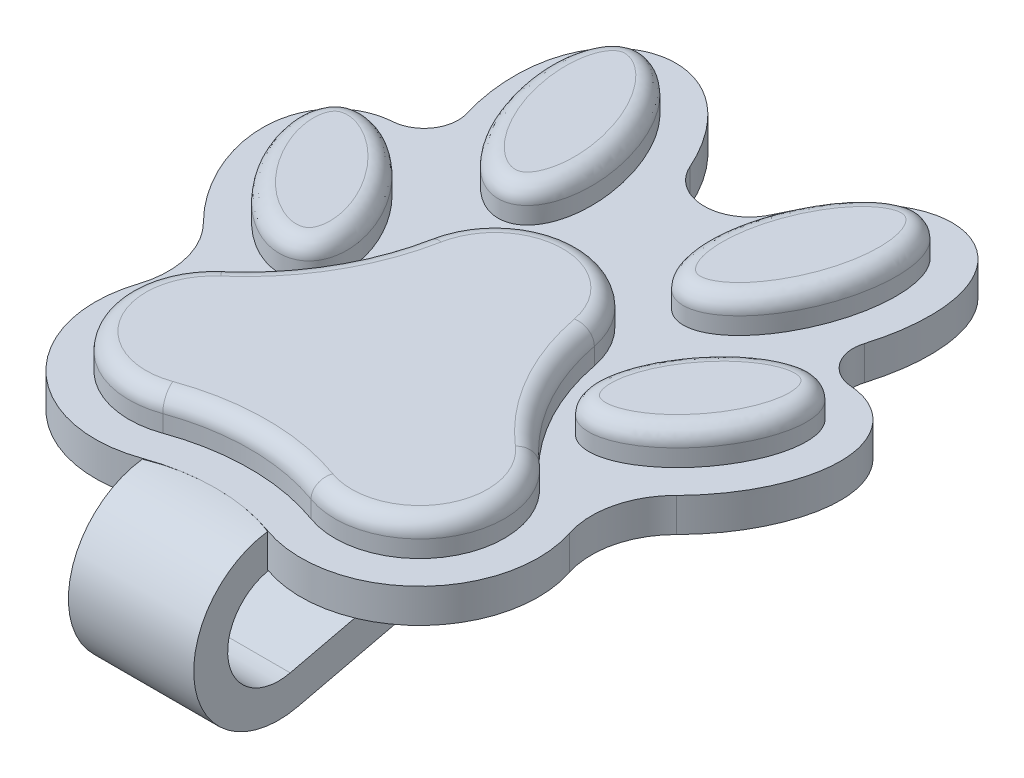
SolidWorks part; units mm, degrees
ref_plane "Front Plane" through (0, 0, 0) normal (0, 0, 1) x (1, 0, 0)
ref_plane "Top Plane" through (0, 0, 0) normal (0, 1, 0) x (1, 0, 0)
ref_plane "Right Plane" through (0, 0, 0) normal (1, 0, 0) x (0, 0, -1)
sketch "Sketch3" plane through (0, 0, 0) normal (0, 1, 0) x (1, 0, 0)
  line L0 (0, 0) -> (0, -27.3757) construction
  line L1 (0, 5) -> (-6.0622, -5.5) construction
  arc A0 (4.9097, 5.9458) -> (-4.9097, 5.9458) centre (0, 5) ccw
  arc A1 (4.3698, -10.2049) -> (9.3361, -1.721) centre (6.0622, -5.5) ccw
  arc A2 (-9.3361, -1.721) -> (-4.3698, -10.2049) centre (-6.0622, -5.5) ccw
  arc A3 (-4.9097, 5.9458) -> (-9.3361, -1.721) centre (-18.1955, 8.5052) cw
  arc A4 (4.9097, 5.9458) -> (9.3361, -1.721) centre (18.1955, 8.5052) ccw
  arc A5 (4.3698, -10.2049) -> (-4.3698, -10.2049) centre (0, -22.3528) ccw
  ellipse E0 centre (11.1505, 5.9458) end of major axis (8.0278, 1.7402) minor radius 2.8576
  ellipse E1 centre (6.7977, 16.2233) end of major axis (8.6857, 21.7116) minor radius 3.0528
  ellipse E2 centre (-11.1505, 5.9458) end of major axis (-14.2732, 10.1515) minor radius 2.8576
  ellipse E3 centre (-6.7977, 16.2233) end of major axis (-8.6857, 21.7116) minor radius 3.0528
  point P12 (0, -2)
  dimension "D1" = 5
  dimension "D3" = 10
  dimension "D4" = 12.91
  dimension "D5" = 13.53
  dimension "D2" = 3
extrude "Boss-Extrude1" add sketch "Sketch3" along normal blind 2
sketch "Sketch4" plane through (0, 0, 0) normal (0, -1, 0) x (1, 0, 0)
  arc A0 (2.4233, -18.8956) -> (-2.4381, -18.9289) centre (0, -19.9916) ccw
  arc A1 (11.7264, -15.0458) -> (13.4953, -12.4721) centre (13.6407, -14.4668) cw
  arc A2 (-13.4941, -12.472) -> (-11.7262, -15.0455) centre (-13.6406, -14.4667) cw
  arc A9 (13.9433, -1.7682) -> (12.7166, 3.3278) centre (17.4698, 1.7763) cw
  arc A10 (-13.9449, -1.7693) -> (-12.7167, 3.3281) centre (-17.4699, 1.7767) ccw
  arc A12 (10.6457, 0.2093) -> (3.6928, 12.0868) centre (6.0622, 5.5) ccw
  arc A13 (-3.6928, 12.0868) -> (3.6928, 12.0868) centre (0, 22.3528) ccw
  arc A14 (-3.6928, 12.0868) -> (-10.6457, 0.2093) centre (-6.0622, 5.5) ccw
  arc A15 (12.7166, 3.3278) -> (3.6928, 12.0868) centre (6.0622, 5.5) ccw
  arc A16 (-3.6928, 12.0868) -> (3.6928, 12.0868) centre (0, 22.3528) ccw
  arc A17 (-3.6928, 12.0868) -> (-12.7167, 3.3281) centre (-6.0622, 5.5) ccw
  spline S0 degree 3 poles (-6.6721, -0.2558) (-7.1625, 0.1084) (-7.5206, 0.2889) (-8.2956, 0.5328) (-8.6948, 0.5901) (-9.5056, 0.5933) (-9.905, 0.5391) (-10.6836, 0.3462) (-11.0669, 0.2055) (-11.7925, -0.1333) (-12.1389, -0.3321) (-12.805, -0.7774) (-13.126, -1.0254) (-14.032, -1.814) (-14.5686, -2.4017) (-15.2846, -3.3646) (-15.509, -3.7015) (-15.9166, -4.39) (-16.1008, -4.7427) (-16.4271, -5.4662) (-16.5693, -5.8369) (-16.804, -6.5998) (-16.897, -6.9958) (-17.0137, -7.7923) (-17.0383, -8.193) (-17.0095, -8.7986) (-16.9886, -9.0011) (-16.9229, -9.3979) (-16.878, -9.5933) (-16.7616, -9.9778) (-16.6894, -10.1681) (-16.5172, -10.5349) (-16.4182, -10.71) (-16.1932, -11.0428) (-16.0666, -11.2012) (-15.7867, -11.4959) (-15.6363, -11.6294) (-15.1546, -11.9898) (-14.7866, -12.1773) (-14.0201, -12.4211) (-13.6128, -12.4808) (-12.8074, -12.4857) (-12.4007, -12.4316) (-11.6212, -12.2391) (-11.2447, -12.1015) (-10.5124, -11.7606) (-10.1621, -11.5594) (-9.4975, -11.1153) (-9.1812, -10.8712) (-8.5762, -10.3453) (-8.2863, -10.0618) (-7.7438, -9.4716) (-7.4899, -9.1639) (-7.0151, -8.5249) (-6.7943, -8.1936) (-6.3869, -7.5061) (-6.1995, -7.1478) (-5.8691, -6.414) (-5.7264, -6.0399) (-5.4926, -5.2748) (-5.4013, -4.883) (-5.2857, -4.0821) (-5.2625, -3.6814) (-5.3028, -2.8793) (-5.3682, -2.4744) (-5.5448, -1.899) (-5.6167, -1.7114) (-5.7897, -1.3456) (-5.8909, -1.1683) (-6.1167, -0.8372) (-6.2422, -0.6816) (-6.5192, -0.3914) (-6.6721, -0.2558) (-7.1625, 0.1084) (-7.5206, 0.2889) knots -0.015625 -0.015625 0 0 0.03125 0.03125 0.0625 0.0625 0.09375 0.09375 0.125 0.125 0.15625 0.15625 0.1875 0.1875 0.25 0.25 0.28125 0.28125 0.3125 0.3125 0.34375 0.34375 0.375 0.375 0.40625 0.40625 0.421875 0.421875 0.4375 0.4375 0.453125 0.453125 0.46875 0.46875 0.484375 0.484375 0.5 0.5 0.53125 0.53125 0.5625 0.5625 0.59375 0.59375 0.625 0.625 0.65625 0.65625 0.6875 0.6875 0.71875 0.71875 0.75 0.75 0.78125 0.78125 0.8125 0.8125 0.84375 0.84375 0.875 0.875 0.90625 0.90625 0.9375 0.9375 0.953125 0.953125 0.96875 0.96875 0.984375 0.984375 1 1 1.03125 1.03125 1.0625 only from (-6.8356, -0.1344) to (-6.8356, -0.1344)
  spline S1 degree 3 poles (-13.9449, -1.7693) (-14.3433, -2.1653) (-14.7093, -2.591) (-15.2846, -3.3646) (-15.509, -3.7015) (-15.9166, -4.39) (-16.1008, -4.7427) (-16.4271, -5.4662) (-16.5693, -5.8369) (-16.804, -6.5998) (-16.897, -6.9958) (-17.0137, -7.7923) (-17.0383, -8.193) (-17.0095, -8.7986) (-16.9886, -9.0011) (-16.9229, -9.3979) (-16.878, -9.5933) (-16.7616, -9.9778) (-16.6894, -10.1681) (-16.5172, -10.5349) (-16.4182, -10.71) (-16.1932, -11.0428) (-16.0666, -11.2012) (-15.7867, -11.4959) (-15.6363, -11.6294) (-15.1546, -11.9898) (-14.7866, -12.1773) (-14.1101, -12.3925) (-13.8027, -12.4494) (-13.4941, -12.472) knots 0.205929 0.205929 0.205929 0.205929 0.25 0.25 0.28125 0.28125 0.3125 0.3125 0.34375 0.34375 0.375 0.375 0.40625 0.40625 0.421875 0.421875 0.4375 0.4375 0.453125 0.453125 0.46875 0.46875 0.484375 0.484375 0.5 0.5 0.53125 0.53125 0.555164 0.555164 0.555164 0.555164
  spline S2 degree 3 poles (-4.054, -8.9143) (-4.6695, -8.7026) (-5.0927, -8.6383) (-5.9592, -8.6547) (-6.3812, -8.7352) (-7.1994, -9.015) (-7.5798, -9.2086) (-8.118, -9.5591) (-8.2928, -9.6869) (-8.6271, -9.9566) (-8.7868, -10.0984) (-9.2469, -10.5418) (-9.5284, -10.8611) (-10.0507, -11.5382) (-10.2913, -11.8964) (-10.9437, -12.9944) (-11.2952, -13.7657) (-11.7119, -14.9748) (-11.8322, -15.3886) (-12.0285, -16.2174) (-12.1052, -16.6342) (-12.2126, -17.4726) (-12.2434, -17.8943) (-12.2484, -18.5312) (-12.2432, -18.7443) (-12.2171, -19.1721) (-12.196, -19.3875) (-12.1068, -20.0256) (-12.0131, -20.4432) (-11.8053, -21.0542) (-11.7243, -21.2556) (-11.5401, -21.6427) (-11.4366, -21.8296) (-11.2037, -22.1885) (-11.0735, -22.3616) (-10.7874, -22.6853) (-10.6333, -22.8343) (-10.3019, -23.1052) (-10.1232, -23.228) (-9.7464, -23.44) (-9.5513, -23.5279) (-9.1477, -23.6685) (-8.9378, -23.7214) (-8.5104, -23.789) (-8.2964, -23.8036) (-7.8677, -23.7969) (-7.6514, -23.7753) (-7.2265, -23.6986) (-7.0189, -23.644) (-6.6123, -23.506) (-6.412, -23.4219) (-6.0259, -23.2305) (-5.8404, -23.1236) (-5.3034, -22.7746) (-4.9696, -22.5029) (-4.3492, -21.9059) (-4.0674, -21.5857) (-3.5474, -20.912) (-3.3093, -20.5584) (-2.8712, -19.8221) (-2.6721, -19.4402) (-2.3168, -18.6665) (-2.1594, -18.2725) (-1.8833, -17.471) (-1.7646, -17.0635) (-1.5679, -16.2341) (-1.4896, -15.81) (-1.3814, -14.9609) (-1.3511, -14.5357) (-1.3459, -13.6835) (-1.371, -13.255) (-1.4922, -12.4026) (-1.5871, -11.9857) (-1.8649, -11.1761) (-2.0505, -10.781) (-2.4015, -10.2444) (-2.5309, -10.0737) (-2.818, -9.751) (-2.9742, -9.6013) (-3.3052, -9.3329) (-3.481, -9.2131) (-3.8547, -9.0039) (-4.054, -8.9143) (-4.6695, -8.7026) (-5.0927, -8.6383) knots -0.015625 -0.015625 0 0 0.03125 0.03125 0.0625 0.0625 0.09375 0.09375 0.109375 0.109375 0.125 0.125 0.15625 0.15625 0.1875 0.1875 0.25 0.25 0.28125 0.28125 0.3125 0.3125 0.34375 0.34375 0.359375 0.359375 0.375 0.375 0.40625 0.40625 0.421875 0.421875 0.4375 0.4375 0.453125 0.453125 0.46875 0.46875 0.484375 0.484375 0.5 0.5 0.515625 0.515625 0.53125 0.53125 0.546875 0.546875 0.5625 0.5625 0.578125 0.578125 0.59375 0.59375 0.625 0.625 0.65625 0.65625 0.6875 0.6875 0.71875 0.71875 0.75 0.75 0.78125 0.78125 0.8125 0.8125 0.84375 0.84375 0.875 0.875 0.90625 0.90625 0.9375 0.9375 0.953125 0.953125 0.96875 0.96875 0.984375 0.984375 1 1 1.03125 1.03125 1.0625 only from (-4.2592, -8.8437) to (-4.2592, -8.8437)
  spline S3 degree 3 poles (-11.7262, -15.0455) (-11.802, -15.2962) (-11.8704, -15.5495) (-12.0285, -16.2174) (-12.1052, -16.6342) (-12.2126, -17.4726) (-12.2434, -17.8943) (-12.2484, -18.5312) (-12.2432, -18.7443) (-12.2171, -19.1721) (-12.196, -19.3875) (-12.1068, -20.0256) (-12.0131, -20.4432) (-11.8053, -21.0542) (-11.7243, -21.2556) (-11.5401, -21.6427) (-11.4366, -21.8296) (-11.2037, -22.1885) (-11.0735, -22.3616) (-10.7874, -22.6853) (-10.6333, -22.8343) (-10.3019, -23.1052) (-10.1232, -23.228) (-9.7464, -23.44) (-9.5513, -23.5279) (-9.1477, -23.6685) (-8.9378, -23.7214) (-8.5104, -23.789) (-8.2964, -23.8036) (-7.8677, -23.7969) (-7.6514, -23.7753) (-7.2265, -23.6986) (-7.0189, -23.644) (-6.6123, -23.506) (-6.412, -23.4219) (-6.0259, -23.2305) (-5.8404, -23.1236) (-5.3034, -22.7746) (-4.9696, -22.5029) (-4.3492, -21.9059) (-4.0674, -21.5857) (-3.5474, -20.912) (-3.3093, -20.5584) (-2.8712, -19.8221) (-2.6721, -19.4402) (-2.4701, -19.0004) (-2.4462, -18.9473) (-2.4226, -18.894) knots 0.262135 0.262135 0.262135 0.262135 0.28125 0.28125 0.3125 0.3125 0.34375 0.34375 0.359375 0.359375 0.375 0.375 0.40625 0.40625 0.421875 0.421875 0.4375 0.4375 0.453125 0.453125 0.46875 0.46875 0.484375 0.484375 0.5 0.5 0.515625 0.515625 0.53125 0.53125 0.546875 0.546875 0.5625 0.5625 0.578125 0.578125 0.59375 0.59375 0.625 0.625 0.65625 0.65625 0.6875 0.6875 0.71875 0.71875 0.723029 0.723029 0.723029 0.723029
  spline S4 degree 3 poles (4.4643, -8.7731) (3.8488, -8.9849) (3.4757, -9.1946) (2.8026, -9.7405) (2.5194, -10.0636) (2.0465, -10.7876) (1.8657, -11.1742) (1.657, -11.7817) (1.5978, -11.99) (1.5002, -12.4082) (1.4615, -12.6182) (1.3716, -13.2508) (1.3462, -13.6758) (1.3508, -14.5309) (1.3815, -14.9613) (1.5427, -16.2283) (1.7401, -17.0526) (2.1554, -18.2622) (2.3151, -18.6624) (2.6703, -19.4366) (2.8661, -19.8124) (3.2973, -20.5394) (3.5325, -20.8908) (3.9203, -21.3961) (4.0555, -21.5609) (4.3393, -21.8821) (4.4885, -22.0389) (4.9514, -22.487) (5.2821, -22.7587) (5.8218, -23.1125) (6.0095, -23.2215) (6.3929, -23.4133) (6.5895, -23.497) (6.9939, -23.6367) (7.2031, -23.693) (7.6277, -23.7722) (7.8409, -23.7949) (8.2688, -23.8046) (8.4853, -23.7914) (8.9127, -23.7268) (9.1206, -23.6761) (9.5253, -23.5386) (9.7233, -23.4512) (10.1019, -23.2416) (10.2796, -23.1214) (10.6134, -22.8524) (10.7706, -22.7023) (11.0584, -22.3805) (11.1885, -22.2097) (11.4242, -21.8507) (11.5304, -21.6612) (11.717, -21.2727) (11.7975, -21.0744) (12.0061, -20.4689) (12.1021, -20.0493) (12.2239, -19.197) (12.2491, -18.7712) (12.2447, -17.9202) (12.2148, -17.4949) (12.1072, -16.6449) (12.0293, -16.2214) (11.8334, -15.3928) (11.7151, -14.9854) (11.4397, -14.1836) (11.2825, -13.7893) (10.9274, -13.0145) (10.7282, -12.6319) (10.2912, -11.896) (10.0534, -11.5421) (9.5333, -10.8671) (9.2499, -10.5447) (8.6299, -9.9472) (8.2987, -9.6769) (7.5816, -9.2096) (7.1922, -9.0123) (6.5854, -8.8051) (6.3784, -8.7502) (5.9535, -8.6724) (5.7383, -8.6505) (5.3122, -8.6425) (5.0999, -8.6562) (4.6766, -8.7212) (4.4643, -8.7731) (3.8488, -8.9849) (3.4757, -9.1946) knots -0.015625 -0.015625 0 0 0.03125 0.03125 0.0625 0.0625 0.09375 0.09375 0.109375 0.109375 0.125 0.125 0.15625 0.15625 0.1875 0.1875 0.25 0.25 0.28125 0.28125 0.3125 0.3125 0.34375 0.34375 0.359375 0.359375 0.375 0.375 0.40625 0.40625 0.421875 0.421875 0.4375 0.4375 0.453125 0.453125 0.46875 0.46875 0.484375 0.484375 0.5 0.5 0.515625 0.515625 0.53125 0.53125 0.546875 0.546875 0.5625 0.5625 0.578125 0.578125 0.59375 0.59375 0.625 0.625 0.65625 0.65625 0.6875 0.6875 0.71875 0.71875 0.75 0.75 0.78125 0.78125 0.8125 0.8125 0.84375 0.84375 0.875 0.875 0.90625 0.90625 0.9375 0.9375 0.953125 0.953125 0.96875 0.96875 0.984375 0.984375 1 1 1.03125 1.03125 1.0625 only from (4.2592, -8.8437) to (4.2592, -8.8437)
  spline S5 degree 3 poles (2.4233, -18.8956) (2.4461, -18.9471) (2.4692, -18.9984) (2.6703, -19.4366) (2.8661, -19.8124) (3.2973, -20.5394) (3.5325, -20.8908) (3.9203, -21.3961) (4.0555, -21.5609) (4.3393, -21.8821) (4.4885, -22.0389) (4.9514, -22.487) (5.2821, -22.7587) (5.8218, -23.1125) (6.0095, -23.2215) (6.3929, -23.4133) (6.5895, -23.497) (6.9939, -23.6367) (7.2031, -23.693) (7.6277, -23.7722) (7.8409, -23.7949) (8.2688, -23.8046) (8.4853, -23.7914) (8.9127, -23.7268) (9.1206, -23.6761) (9.5253, -23.5386) (9.7233, -23.4512) (10.1019, -23.2416) (10.2796, -23.1214) (10.6134, -22.8524) (10.7706, -22.7023) (11.0584, -22.3805) (11.1885, -22.2097) (11.4242, -21.8507) (11.5304, -21.6612) (11.717, -21.2727) (11.7975, -21.0744) (12.0061, -20.4689) (12.1021, -20.0493) (12.2239, -19.197) (12.2491, -18.7712) (12.2447, -17.9202) (12.2148, -17.4949) (12.1072, -16.6449) (12.0293, -16.2214) (11.8707, -15.5507) (11.8023, -15.297) (11.7264, -15.0458) knots 0.277126 0.277126 0.277126 0.277126 0.28125 0.28125 0.3125 0.3125 0.34375 0.34375 0.359375 0.359375 0.375 0.375 0.40625 0.40625 0.421875 0.421875 0.4375 0.4375 0.453125 0.453125 0.46875 0.46875 0.484375 0.484375 0.5 0.5 0.515625 0.515625 0.53125 0.53125 0.546875 0.546875 0.5625 0.5625 0.578125 0.578125 0.59375 0.59375 0.625 0.625 0.65625 0.65625 0.6875 0.6875 0.71875 0.71875 0.738088 0.738088 0.738088 0.738088
  spline S6 degree 3 poles (6.999, -0.013) (6.5086, -0.3771) (6.2322, -0.6677) (5.7746, -1.339) (5.6043, -1.7046) (5.3667, -2.4798) (5.303, -2.8778) (5.2625, -3.6789) (5.2863, -4.0865) (5.4008, -4.8792) (5.4909, -5.2682) (5.7245, -6.0346) (5.869, -6.4137) (6.3619, -7.509) (6.7692, -8.1926) (7.4839, -9.1566) (7.7415, -9.4688) (8.2827, -10.0581) (8.567, -10.3365) (9.1652, -10.8581) (9.4789, -11.1015) (10.1413, -11.5468) (10.4935, -11.7503) (11.2222, -12.0925) (11.5987, -12.2319) (12.1867, -12.3795) (12.3866, -12.4181) (12.7854, -12.4699) (12.9855, -12.4835) (13.3872, -12.4832) (13.5902, -12.4692) (13.9912, -12.4105) (14.1875, -12.3663) (14.5711, -12.2472) (14.7593, -12.1718) (15.1224, -11.9891) (15.2937, -11.8838) (15.778, -11.5269) (16.064, -11.2288) (16.519, -10.5657) (16.694, -10.193) (16.9317, -9.4235) (16.9974, -9.0185) (17.0386, -8.2167) (17.0159, -7.8164) (16.9014, -7.0169) (16.81, -6.6233) (16.5771, -5.8587) (16.435, -5.4853) (16.1066, -4.7541) (15.9191, -4.3945) (15.511, -3.7045) (15.2899, -3.3725) (14.8155, -2.7332) (14.5622, -2.4259) (14.0219, -1.8371) (13.7332, -1.5541) (13.1263, -1.0256) (12.8094, -0.7807) (12.1447, -0.3357) (11.796, -0.1349) (11.0629, 0.2074) (10.686, 0.3455) (9.9065, 0.5389) (9.5, 0.5934) (8.8981, 0.5909) (8.6977, 0.5763) (8.2975, 0.5164) (8.0986, 0.4709) (7.7163, 0.3505) (7.5311, 0.2754) (7.1731, 0.0941) (6.999, -0.013) (6.5086, -0.3771) (6.2322, -0.6677) knots -0.015625 -0.015625 0 0 0.03125 0.03125 0.0625 0.0625 0.09375 0.09375 0.125 0.125 0.15625 0.15625 0.1875 0.1875 0.25 0.25 0.28125 0.28125 0.3125 0.3125 0.34375 0.34375 0.375 0.375 0.40625 0.40625 0.421875 0.421875 0.4375 0.4375 0.453125 0.453125 0.46875 0.46875 0.484375 0.484375 0.5 0.5 0.53125 0.53125 0.5625 0.5625 0.59375 0.59375 0.625 0.625 0.65625 0.65625 0.6875 0.6875 0.71875 0.71875 0.75 0.75 0.78125 0.78125 0.8125 0.8125 0.84375 0.84375 0.875 0.875 0.90625 0.90625 0.9375 0.9375 0.953125 0.953125 0.96875 0.96875 0.984375 0.984375 1 1 1.03125 1.03125 1.0625 only from (6.8356, -0.1344) to (6.8356, -0.1344)
  spline S7 degree 3 poles (13.4953, -12.4721) (13.594, -12.4649) (13.6927, -12.4542) (13.9912, -12.4105) (14.1875, -12.3663) (14.5711, -12.2472) (14.7593, -12.1718) (15.1224, -11.9891) (15.2937, -11.8838) (15.778, -11.5269) (16.064, -11.2288) (16.519, -10.5657) (16.694, -10.193) (16.9317, -9.4235) (16.9974, -9.0185) (17.0386, -8.2167) (17.0159, -7.8164) (16.9014, -7.0169) (16.81, -6.6233) (16.5771, -5.8587) (16.435, -5.4853) (16.1066, -4.7541) (15.9191, -4.3945) (15.511, -3.7045) (15.2899, -3.3725) (14.8155, -2.7332) (14.5622, -2.4259) (14.179, -2.0082) (14.0626, -1.887) (13.9433, -1.7682) knots 0.445483 0.445483 0.445483 0.445483 0.453125 0.453125 0.46875 0.46875 0.484375 0.484375 0.5 0.5 0.53125 0.53125 0.5625 0.5625 0.59375 0.59375 0.625 0.625 0.65625 0.65625 0.6875 0.6875 0.71875 0.71875 0.75 0.75 0.78125 0.78125 0.794335 0.794335 0.794335 0.794335
  arc M8 (-9.3361, 1.721) -> (-4.9097, -5.9458) centre (-18.1955, -8.5052) cw
  arc M9 (-4.9097, -5.9458) -> (4.9097, -5.9458) centre (0, -5) ccw
  arc M10 (4.9097, -5.9458) -> (9.3361, 1.721) centre (18.1955, -8.5052) cw
  arc M11 (9.3361, 1.721) -> (4.3698, 10.2049) centre (6.0622, 5.5) ccw
  arc M12 (4.3698, 10.2049) -> (-4.3698, 10.2049) centre (0, 22.3528) cw
  arc M13 (-4.3698, 10.2049) -> (-9.3361, 1.721) centre (-6.0622, 5.5) ccw
  dimension "D6" = 5
  dimension "D7" = 2
  dimension "D1" = 2
  dimension "D2" = 2
  dimension "D3" = 2
  dimension "D4" = 2
  dimension "D5" = 2
extrude "Boss-Extrude2" add sketch "Sketch4" along normal blind 2 contours A1 S7 A9 A15 A16 A17 A10 S1 A2 S3 A0 S5 M8 M13 M12 M11 M10 M9 | M13 M8 M9 M10 M11 M12
fillet "Fillet1" radius 1 4 edges at (14.2732, 2, -10.1515) (8.6857, 2, -21.7116) (-8.6857, 2, -21.7116) (-14.2732, 2, -10.1515)
fillet "Fillet2" radius 1 6 edges at (6.4781, 2, -1.7402) (10.3772, 2, 8.026) (0, 2, 9.4428) (-10.3772, 2, 8.026) (-6.4781, 2, -1.7402) (0, 2, -10)
sketch "Sketch5" plane through (0, 0, 0) normal (1, 0, 0) x (0, 0, -1)
  line L1 (17.1087, -5.7418) -> (17.332, -3.7543)
  line L2 (-12.5, -2) -> (-3.3278, -2) construction
  line L3 (-10.757, -7.9205) -> (10.332, -2.9678)
  line L4 (10.332, -2.9678) -> (17.332, -3.7543)
  line L5 (-10.2997, -9.8676) -> (10.4525, -4.994)
  line L6 (10.4525, -4.994) -> (17.1087, -5.7418)
  line L7 (-11.4428, 0) -> (-11.4428, -2)
  arc A0 (-11.4428, -2) -> (-10.757, -7.9205) centre (-11.4428, -5) ccw
  arc A1 (-11.4428, 0) -> (-10.2997, -9.8676) centre (-11.4428, -5) ccw
  dimension "D1" = 3
  dimension "D2" = 7
  dimension "D3" = 2
extrude "Boss-Extrude3" add sketch "Sketch5" along normal up to vertex (3.6928 mm away) and the other way up to vertex (3.6928 mm away) up to point (3.6928, 0, 12.0868)
